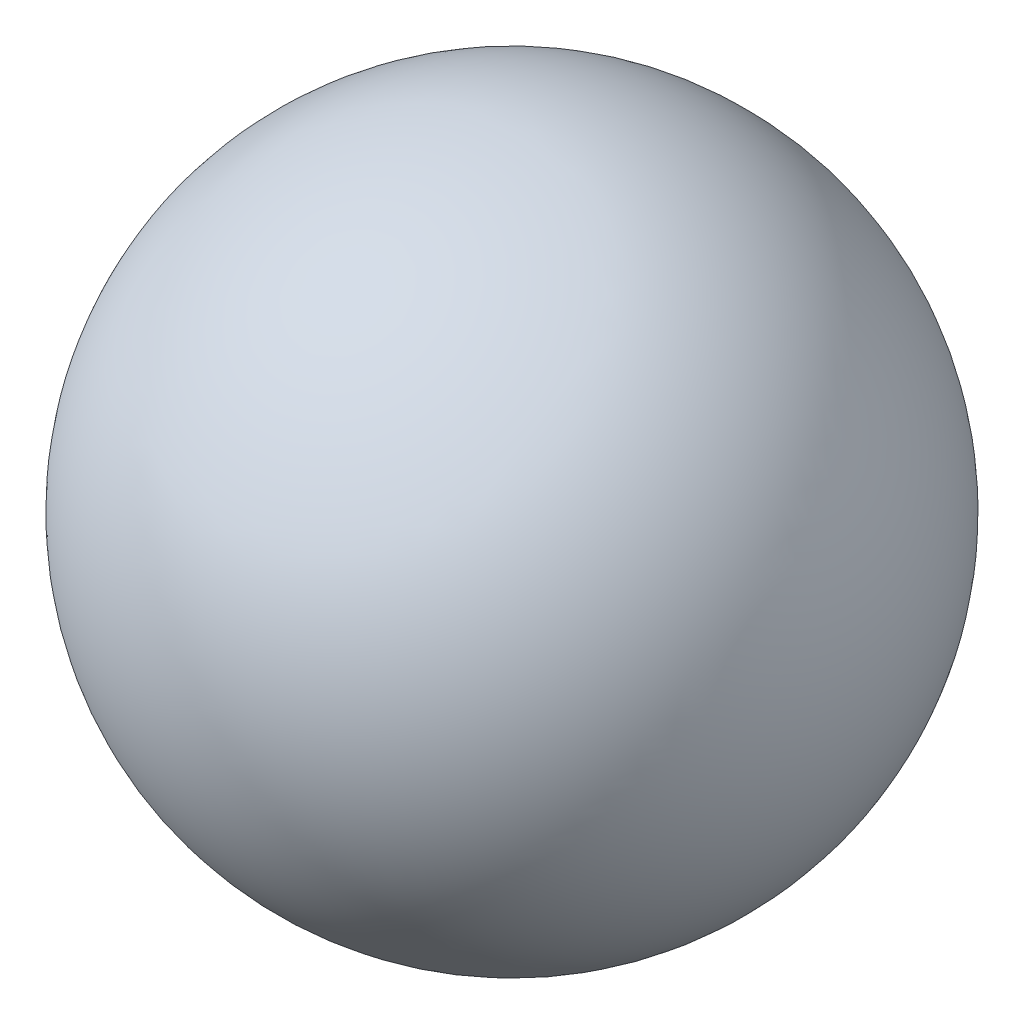
SolidWorks part; units mm, degrees
ref_plane "Front Plane" through (0, 0, 0) normal (0, 0, 1) x (1, 0, 0)
ref_plane "Top Plane" through (0, 0, 0) normal (0, 1, 0) x (1, 0, 0)
ref_plane "Right Plane" through (0, 0, 0) normal (1, 0, 0) x (0, 0, -1)
sketch "Sketch1" plane through (0, 0, 0) normal (0, 0, 1) x (1, 0, 0)
  line L1 (-21.35, 0) -> (21.35, 0)
  arc A0 (21.35, 0) -> (-21.35, 0) centre (0, 0) ccw
  dimension "D1" = 21.35
revolve "Revolve1" add sketch "Sketch1" angle 360 about L1
